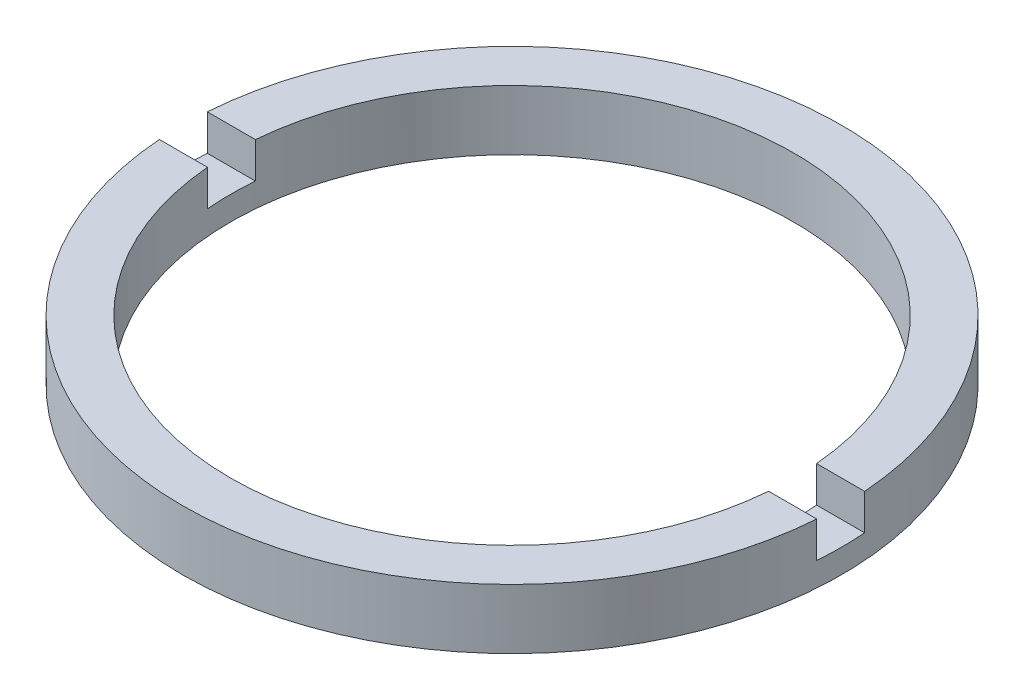
SolidWorks part; units mm, degrees
ref_plane "前视基准面" through (0, 0, 0) normal (0, 0, 1) x (1, 0, 0)
ref_plane "上视基准面" through (0, 0, 0) normal (0, 1, 0) x (1, 0, 0)
ref_plane "右视基准面" through (0, 0, 0) normal (1, 0, 0) x (0, 0, -1)
sketch "草图1" plane through (0, 0, 0) normal (0, 0, 1) x (1, 0, 0)
  line L0 (0, 56.2608) -> (0, -99.1922) construction
  line L1 (11.75, -1.9642) -> (13.75, -1.9642)
  line L4 (13.75, -1.9642) -> (13.75, -4.4642)
  line L5 (11.75, -4.4642) -> (11.75, -1.9642)
  line L7 (11.75, -4.4642) -> (13.75, -4.4642)
  dimension "D1" = 2.5
  dimension "D2" = 13.75
  dimension "D3" = 11.75
revolve "旋转1" add sketch "草图1" angle 360 about L0
cosmetic thread "装饰螺纹线1"
sketch "草图2" plane through (0, -1.9642, 0) normal (0, 1, 0) x (1, 0, 0)
  line L0 (-28.67, 0) -> (29.9422, 0) construction
  line L2 (-26.8525, 1) -> (26.8525, 1)
  line L3 (-26.8525, 1) -> (-26.8525, -1)
  line L4 (-26.8525, -1) -> (26.8525, -1)
  line L5 (26.8525, 1) -> (26.8525, -1)
  line L6 (-26.8525, 1) -> (26.8525, -1) construction
  line L7 (-26.8525, -1) -> (26.8525, 1) construction
  point P3 (0, 0)
  dimension "D1" = 2
extrude "切除-拉伸1" cut sketch "草图2" against normal blind 1.5
